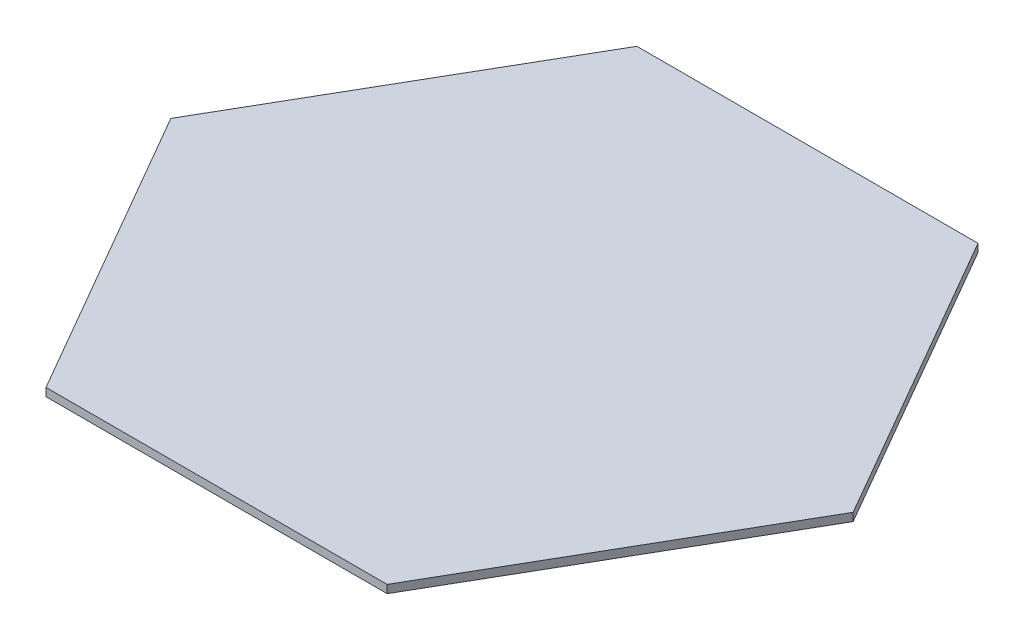
SolidWorks part; units mm, degrees
material "Thornel Mat VMA"
ref_plane "Alzado" through (0, 0, 0) normal (0, 0, 1) x (1, 0, 0)
ref_plane "Planta" through (0, 0, 0) normal (0, 1, 0) x (1, 0, 0)
ref_plane "Vista lateral" through (0, 0, 0) normal (1, 0, 0) x (0, 0, -1)
sketch "Croquis1" plane through (0, 0, 0) normal (0, 1, 0) x (1, 0, 0)
  line L1 (63.5085, -110) -> (127.0171, 0)
  line L2 (127.0171, 0) -> (63.5085, 110)
  line L3 (63.5085, 110) -> (-63.5085, 110)
  line L4 (-63.5085, 110) -> (-127.0171, 0)
  line L5 (-127.0171, 0) -> (-63.5085, -110)
  line L6 (-63.5085, -110) -> (63.5085, -110)
  circle A0 centre (0, 0) radius 110 construction
  dimension "D1" = 220
extrude "Saliente-Extruir1" add sketch "Croquis1" along normal blind 3
